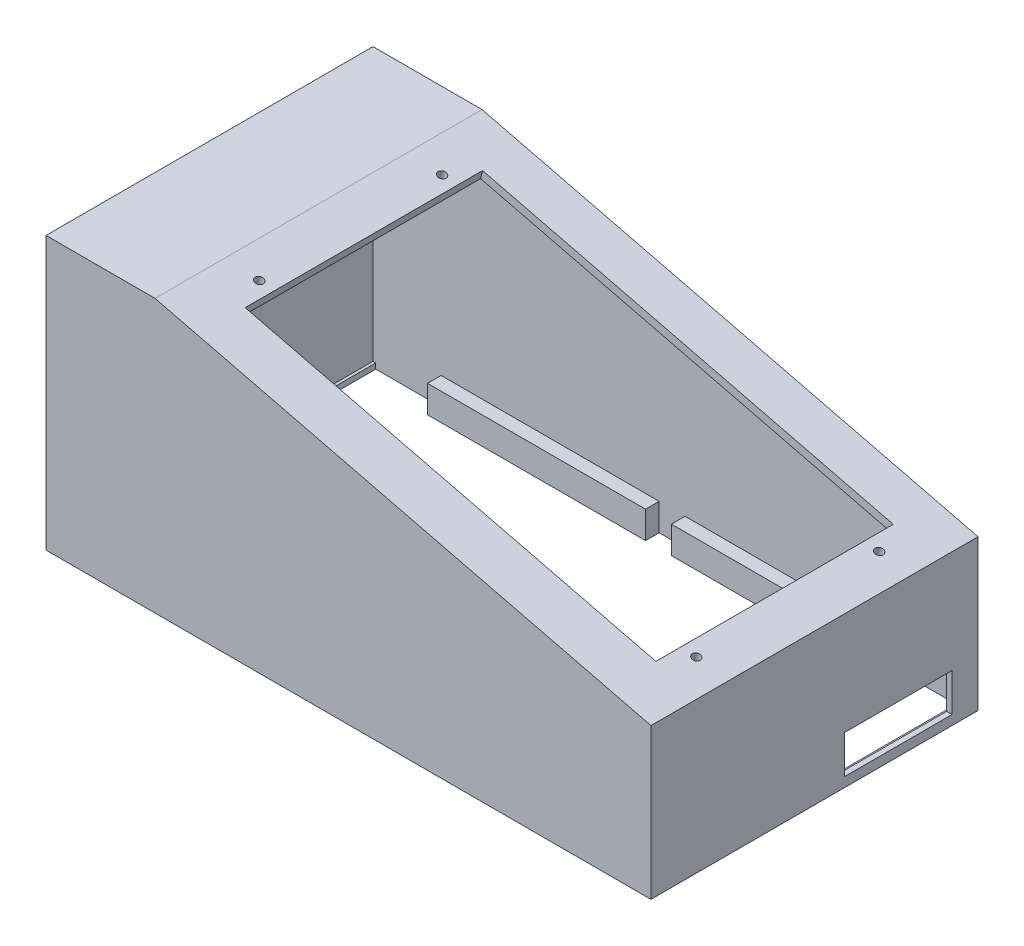
SolidWorks part; units mm, degrees
ref_plane "Alzado" through (0, 0, 0) normal (0, 0, 1) x (1, 0, 0)
ref_plane "Planta" through (0, 0, 0) normal (0, 1, 0) x (1, 0, 0)
ref_plane "Vista lateral" through (0, 0, 0) normal (1, 0, 0) x (0, 0, -1)
sketch "Sketch1" plane through (0, 0, 0) normal (0, 0, 1) x (1, 0, 0)
  line L0 (-127.5824, -37.8043) -> (94.4176, -32.5631) construction
  line L1 (94.4176, -32.5631) -> (94.4176, 17.4369)
  line L2 (94.4176, -32.5631) -> (92.4176, -32.6104)
  line L3 (92.4176, -32.6104) -> (92.4176, 15.3896)
  line L4 (-127.5824, -37.8043) -> (-127.5824, 62.1957)
  line L5 (-127.5824, 62.1957) -> (-87.5824, 62.1957)
  line L6 (-87.5824, 62.1957) -> (94.4176, 17.4369)
  line L7 (-127.5824, -37.8043) -> (-125.5824, -37.7571)
  line L8 (-125.5824, -37.7571) -> (-125.5824, 60.2429)
  line L9 (-125.5824, 60.2429) -> (-88.0168, 60.2429)
  line L11 (-88.0168, 60.2429) -> (92.4176, 15.8691)
  line L12 (92.4176, 15.8691) -> (92.4176, 15.3896)
  dimension "D1" = 222
  dimension "D2" = 50
  dimension "D3" = 2
  dimension "D4" = 100
  dimension "D5" = 40
  dimension "D6" = 48
  dimension "D7" = 98
  dimension "D8" = 2
  dimension "D9" = 2
extrude "Boss-Extrude1" add sketch "Sketch1" along normal blind 118
sketch "Sketch2" plane through (-127.5824, 0, 0) normal (-1, 0, 0) x (0, 0, 1)
  line L1 (118, -37.8043) -> (50, -37.8043)
  line L2 (118, -37.8043) -> (118, -27.8043)
  line L3 (118, -27.8043) -> (50, -27.8043)
  line L4 (50, -37.8043) -> (50, -27.8043)
  dimension "D1" = 68
  dimension "D2" = 10
extrude "Boss-Extrude2" add sketch "Sketch2" against normal blind 12
sketch "Sketch4" plane through (0, 0, 118) normal (0, 0, 1) x (1, 0, 0)
  line L1 (94.4176, -32.5631) -> (92.4176, -32.5631)
  line L2 (94.4176, -32.5631) -> (94.4176, -37.8043)
  line L3 (94.4176, -37.8043) -> (92.4176, -37.8043)
  line L4 (92.4176, -32.5631) -> (92.4176, -37.8043)
extrude "Boss-Extrude4" add sketch "Sketch4" against normal up to vertex (118 mm away)
sketch "Sketch5" plane through (94.4176, 0, 0) normal (1, 0, 0) x (0, 0, -1)
  line L0 (0, -37.8043) -> (0, 17.4369) construction
  line L1 (-9.5, -34.3043) -> (-49.5, -34.3043)
  line L2 (-9.5, -34.3043) -> (-9.5, -20.3043)
  line L3 (-9.5, -20.3043) -> (-49.5, -20.3043)
  line L4 (-49.5, -34.3043) -> (-49.5, -20.3043)
  line L5 (0, -37.8043) -> (-118, -37.8043) construction
  dimension "D1" = 9.5
  dimension "D2" = 3.5
  dimension "D3" = 14
  dimension "D4" = 40
extrude "Cut-Extrude1" cut sketch "Sketch5" against normal blind 12
sketch "Sketch6" plane through (94.4176, 0, 0) normal (1, 0, 0) x (0, 0, -1)
  line L0 (-49.5, -34.3043) -> (-9.5, -34.3043) construction
  line L1 (-49.5, -20.3043) -> (-49, -20.3043)
  line L2 (-49.5, -20.3043) -> (-49.5, -34.3043)
  line L3 (-49.5, -34.3043) -> (-49, -34.3043)
  line L4 (-49, -20.3043) -> (-49, -34.3043)
  dimension "D1" = 0.5
extrude "Boss-Extrude5" add sketch "Sketch6" against normal up to vertex
sketch "Sketch7" plane through (92.4176, 0, 0) normal (-1, 0, 0) x (0, 0, 1)
  line L0 (0, 15.8691) -> (0, -37.8043) construction
  line L1 (118, -37.8043) -> (0, -37.8043)
  line L2 (118, -37.8043) -> (118, -35.8043)
  line L3 (118, -35.8043) -> (0, -35.8043)
  line L4 (0, -37.8043) -> (0, -35.8043)
  dimension "D1" = 2
extrude "Boss-Extrude6" add sketch "Sketch7" along normal blind 2
sketch "Sketch8" plane through (0, 0, 50) normal (0, 0, -1) x (-1, 0, 0)
  line L0 (127.5824, -37.8043) -> (125.5824, -37.8043)
  line L1 (115.5824, -37.8043) -> (127.5824, -37.8043) construction
  line L2 (125.5824, -37.8043) -> (125.5824, -37.1545)
  line L3 (125.5824, -27.8043) -> (125.5824, -37.7571) construction
  line L4 (125.5824, -37.1545) -> (127.5824, -37.1545)
  line L5 (127.5824, 62.1957) -> (127.5824, -37.8043) construction
  line L6 (127.5824, -37.1545) -> (127.5824, -37.8043)
extrude "Boss-Extrude7" add sketch "Sketch8" along normal up to vertex (50 mm away)
sketch "Sketch10" plane through (0, 0, 0) normal (0, 0, -1) x (-1, 0, 0)
  line L0 (-94.4176, 17.4369) -> (87.5824, 62.1957)
  line L1 (87.5824, 62.1957) -> (127.5824, 62.1957)
  line L2 (127.5824, 62.1957) -> (127.5824, -37.8043)
  line L3 (127.5824, -37.8043) -> (-94.4176, -37.8043)
  line L4 (-94.4176, -37.8043) -> (-94.4176, 17.4369)
extrude "Boss-Extrude8" add sketch "Sketch10" against normal blind 2
sketch "Sketch11" plane through (0, 0, 2) normal (0, 0, 1) x (1, 0, 0)
  line L0 (94.4176, -37.8043) -> (94.4176, 17.4369) construction
  line L1 (94.4176, -35.8043) -> (-127.5824, -35.8043)
  line L2 (94.4176, -35.8043) -> (94.4176, -37.8043)
  line L3 (94.4176, -37.8043) -> (-127.5824, -37.8043)
  line L4 (-127.5824, -35.8043) -> (-127.5824, -37.8043)
extrude "Boss-Extrude9" add sketch "Sketch11" along normal blind 2
sketch "Sketch13" plane through (-127.5824, 0, 0) normal (-1, 0, 0) x (0, 0, 1)
  line L0 (118, 62.1957) -> (118, -37.8043) construction
  line L1 (0, -37.8043) -> (118, -37.8043)
  line L2 (0, -37.8043) -> (0, -35.8043)
  line L3 (0, -35.8043) -> (118, -35.8043)
  line L4 (118, -37.8043) -> (118, -35.8043)
  dimension "D1" = 2
extrude "Boss-Extrude10" add sketch "Sketch13" against normal blind 4
sketch "Sketch14" plane through (0, -35.8043, 0) normal (0, 1, 0) x (1, 0, 0)
  line L1 (-123.5824, -50) -> (-124.5824, -50)
  line L2 (-123.5824, -50) -> (-123.5824, -4)
  line L3 (-123.5824, -4) -> (-124.5824, -4)
  line L4 (-124.5824, -50) -> (-124.5824, -4)
  dimension "D1" = 1
extrude "Cut-Extrude2" cut sketch "Sketch14" against normal blind 4
sketch "Sketch15" plane through (0, -37.8043, 0) normal (0, -1, 0) x (1, 0, 0)
  line L1 (-124.5824, 4) -> (90.4176, 4)
  line L2 (-124.5824, 4) -> (-124.5824, 3)
  line L3 (-124.5824, 3) -> (90.4176, 3)
  line L4 (90.4176, 4) -> (90.4176, 3)
  dimension "D1" = 1
extrude "Cut-Extrude3" cut sketch "Sketch15" against normal blind 4
sketch "Sketch16" plane through (0, -37.8043, 0) normal (0, -1, 0) x (1, 0, 0)
  line L1 (-124.5824, 3) -> (90.4176, 3)
  line L2 (-124.5824, 3) -> (-124.5824, 2)
  line L3 (-124.5824, 2) -> (90.4176, 2)
  line L4 (90.4176, 3) -> (90.4176, 2)
  dimension "D1" = 1
extrude "Cut-Extrude4" cut sketch "Sketch16" against normal blind 4
sketch "Sketch17" plane through (9.4284, 38.338, 0) normal (0.2388, 0.9711, 0) x (0.9711, -0.2388, 0)
  line L0 (87.5215, -118) -> (-99.9014, -118) construction
  line L1 (-83.7914, -15.45) -> (71.4086, -15.45)
  line L2 (-83.7914, -15.45) -> (-83.7914, -102.55)
  line L3 (-83.7914, -102.55) -> (71.4086, -102.55)
  line L4 (71.4086, -15.45) -> (71.4086, -102.55)
  line L6 (-99.9014, -118) -> (-99.9014, 0) construction
  dimension "D1" = 87.1
  dimension "D2" = 155.2
  dimension "D3" = 15.45
  dimension "D4" = 16.11
extrude "Cut-Extrude5" cut sketch "Sketch17" against normal blind 4 contours L2 L3 L4 L1
sketch "Sketch18" plane through (8.9508, 36.3959, 0) normal (-0.2388, -0.9711, 0) x (0.9711, -0.2388, 0)
  line L0 (-83.7914, 15.45) -> (-83.7914, 102.55) construction
  line L1 (-93.7914, 107.55) -> (81.4086, 107.55)
  line L2 (-93.7914, 107.55) -> (-93.7914, 10.45)
  line L3 (-93.7914, 10.45) -> (81.4086, 10.45)
  line L4 (81.4086, 107.55) -> (81.4086, 10.45)
  line L5 (-93.7914, 107.55) -> (81.4086, 10.45) construction
  line L6 (-93.7914, 10.45) -> (81.4086, 107.55) construction
  line L7 (71.4086, 15.45) -> (71.4086, 102.55) construction
  line L8 (-83.7914, 15.45) -> (71.4086, 15.45) construction
  line L9 (-83.7914, 102.55) -> (71.4086, 102.55) construction
  point P0 (-6.1914, 59)
  dimension "D1" = 10
  dimension "D2" = 10
  dimension "D3" = 5
  dimension "D4" = 5
extrude "Boss-Extrude11" add sketch "Sketch18" along normal blind 1
sketch "Sketch19" plane through (8.9508, 36.3959, 0) normal (0.2388, 0.9711, 0) x (0.9711, -0.2388, 0)
  line L0 (-83.7914, -102.55) -> (71.4086, -102.55) construction
  line L1 (-83.7914, -15.45) -> (71.4086, -15.45)
  line L2 (-83.7914, -15.45) -> (-83.7914, -102.55)
  line L3 (-83.7914, -102.55) -> (71.4086, -102.55)
  line L4 (71.4086, -15.45) -> (71.4086, -102.55)
  line L5 (71.4086, -15.45) -> (71.4086, -102.55) construction
extrude "Cut-Extrude6" cut sketch "Sketch19" against normal blind 1
sketch "Sketch20" plane through (8.7119, 35.4248, 0) normal (-0.2388, -0.9711, 0) x (0.9711, -0.2388, 0)
  line L0 (81.4086, 107.55) -> (-93.7914, 107.55) construction
  line L1 (-83.7914, 15.45) -> (-83.7914, 102.55) construction
  line L2 (-93.7914, 10.45) -> (81.4086, 10.45) construction
  line L3 (71.4086, 102.55) -> (71.4086, 15.45) construction
  circle A0 centre (-88.7914, 92.55) radius 1.5
  circle A1 centre (-88.7914, 25.45) radius 1.5
  circle A2 centre (76.4086, 25.45) radius 1.5
  circle A3 centre (76.4086, 92.55) radius 1.5
  dimension "D1" = 15
  dimension "D3" = 15
  dimension "D4" = 5
  dimension "D2" = 5
  dimension "D5" = 15
extrude "Cut-Extrude7" cut sketch "Sketch20" against normal through all
sketch "Sketch21" plane through (0, 0, 0) normal (0, 0, -1) x (-1, 0, 0)
  line L0 (127.5824, -37.8043) -> (100.5824, -37.8043) construction
  line L1 (127.5824, -37.8043) -> (-94.4176, -37.8043) construction
  line L3 (100.5824, -37.8043) -> (20.5824, -37.8043)
  line L4 (100.5824, -37.8043) -> (100.5824, -27.8043)
  line L5 (100.5824, -27.8043) -> (20.5824, -27.8043)
  line L6 (20.5824, -37.8043) -> (20.5824, -27.8043)
  dimension "D1" = 27
  dimension "D2" = 10
  dimension "D3" = 80
extrude "Boss-Extrude12" add sketch "Sketch21" against normal blind 12
sketch "Sketch22" plane through (0, -37.8043, 0) normal (0, -1, 0) x (1, 0, 0)
  line L0 (-100.5824, 12) -> (-100.5824, 2) construction
  line L1 (-20.5824, 12) -> (-100.5824, 12)
  line L2 (-20.5824, 12) -> (-20.5824, 7)
  line L3 (-20.5824, 7) -> (-100.5824, 7)
  line L4 (-100.5824, 12) -> (-100.5824, 7)
extrude "Cut-Extrude8" cut sketch "Sketch22" against normal blind 12
sketch "Sketch23" plane through (94.4176, 0, 0) normal (1, 0, 0) x (0, 0, -1)
  line L0 (0, -37.8043) -> (-118, -37.8043) construction
  line L1 (-66, -37.8043) -> (-56, -37.8043)
  line L2 (-66, -37.8043) -> (-66, -27.8043)
  line L3 (-66, -27.8043) -> (-56, -27.8043)
  line L4 (-56, -37.8043) -> (-56, -27.8043)
  line L5 (0, -37.8043) -> (0, 17.4369) construction
  dimension "D1" = 10
  dimension "D2" = 10
  dimension "D3" = 56
extrude "Boss-Extrude13" add sketch "Sketch23" against normal blind 12
sketch "Sketch24" plane through (0, -37.8043, 0) normal (0, -1, 0) x (1, 0, 0)
  line L0 (94.4176, 0) -> (94.4176, 118) construction
  line L1 (82.4176, 56) -> (94.4176, 56)
  line L2 (82.4176, 56) -> (82.4176, 52)
  line L3 (82.4176, 52) -> (94.4176, 52)
  line L4 (94.4176, 56) -> (94.4176, 52)
  dimension "D1" = 4
extrude "Boss-Extrude14" add sketch "Sketch24" against normal up to vertex
sketch "Sketch25" plane through (0, -37.8043, 0) normal (0, -1, 0) x (1, 0, 0)
  line L0 (90.4176, 2) -> (90.4176, 52) construction
  line L1 (82.4176, 52) -> (90.4176, 52)
  line L2 (82.4176, 52) -> (82.4176, 51)
  line L3 (82.4176, 51) -> (90.4176, 51)
  line L4 (90.4176, 52) -> (90.4176, 51)
  dimension "D1" = 1
extrude "Boss-Extrude15" add sketch "Sketch25" against normal up to vertex
sketch "Sketch27" plane through (0, 0, 2) normal (0, 0, 1) x (1, 0, 0)
  line L0 (-20.5824, -37.8043) -> (90.4176, -37.8043) construction
  line L1 (-11.0824, -27.8043) -> (68.9176, -27.8043)
  line L2 (-11.0824, -27.8043) -> (-11.0824, -37.8043)
  line L3 (-11.0824, -37.8043) -> (68.9176, -37.8043)
  line L4 (68.9176, -27.8043) -> (68.9176, -37.8043)
  dimension "D1" = 9.5
  dimension "D2" = 80
extrude "Boss-Extrude16" add sketch "Sketch27" along normal up to vertex (5 mm away) up to point (-20.5824, -27.8043, 7)
sketch "Sketch28" plane through (0, 0, 118) normal (0, 0, 1) x (1, 0, 0)
  line L0 (-127.5824, -37.8043) -> (94.4176, -37.8043)
  line L1 (94.4176, -37.8043) -> (94.4176, 17.4369)
  line L2 (94.4176, 17.4369) -> (-87.5824, 62.1957)
  line L3 (-87.5824, 62.1957) -> (-127.5824, 62.1957)
  line L4 (-127.5824, 62.1957) -> (-127.5824, -37.8043)
extrude "Boss-Extrude17" add sketch "Sketch28" along normal blind 2
sketch "Sketch30" plane through (0, -37.8043, 0) normal (0, -1, 0) x (1, 0, 0)
  line L0 (-125.5824, 118) -> (-88.0168, 118) construction
  line L1 (-100.5824, 118) -> (-20.5824, 118)
  line L2 (-100.5824, 118) -> (-100.5824, 108)
  line L3 (-100.5824, 108) -> (-20.5824, 108)
  line L4 (-20.5824, 118) -> (-20.5824, 108)
  dimension "D1" = 80
extrude "Boss-Extrude18" add sketch "Sketch30" against normal blind 10
sketch "Sketch31" plane through (0, 0, 118) normal (0, 0, -1) x (-1, 0, 0)
  line L0 (20.5824, -37.8043) -> (-90.4176, -37.8043) construction
  line L1 (10.5824, -37.8043) -> (-39.4176, -37.8043)
  line L2 (10.5824, -37.8043) -> (10.5824, -25.9337)
  line L3 (10.5824, -25.9337) -> (-39.4176, -25.9337)
  line L4 (-39.4176, -37.8043) -> (-39.4176, -25.9337)
  line L5 (20.5824, -27.8043) -> (20.5824, -37.8043) construction
  dimension "D1" = 50
  dimension "D2" = 10
extrude "Boss-Extrude20" add sketch "Sketch31" along normal up to vertex (10 mm away) up to point (-20.5824, -27.8043, 108)
sketch "Sketch32" plane through (0, 0, 108) normal (0, 0, -1) x (-1, 0, 0)
  line L1 (10.5824, -25.9337) -> (-39.4176, -25.9337)
  line L2 (10.5824, -25.9337) -> (10.5824, -27.8037)
  line L3 (10.5824, -27.8037) -> (-39.4176, -27.8037)
  line L4 (-39.4176, -25.9337) -> (-39.4176, -27.8037)
  dimension "D1" = 1.87
extrude "Cut-Extrude9" cut sketch "Sketch32" against normal blind 10
